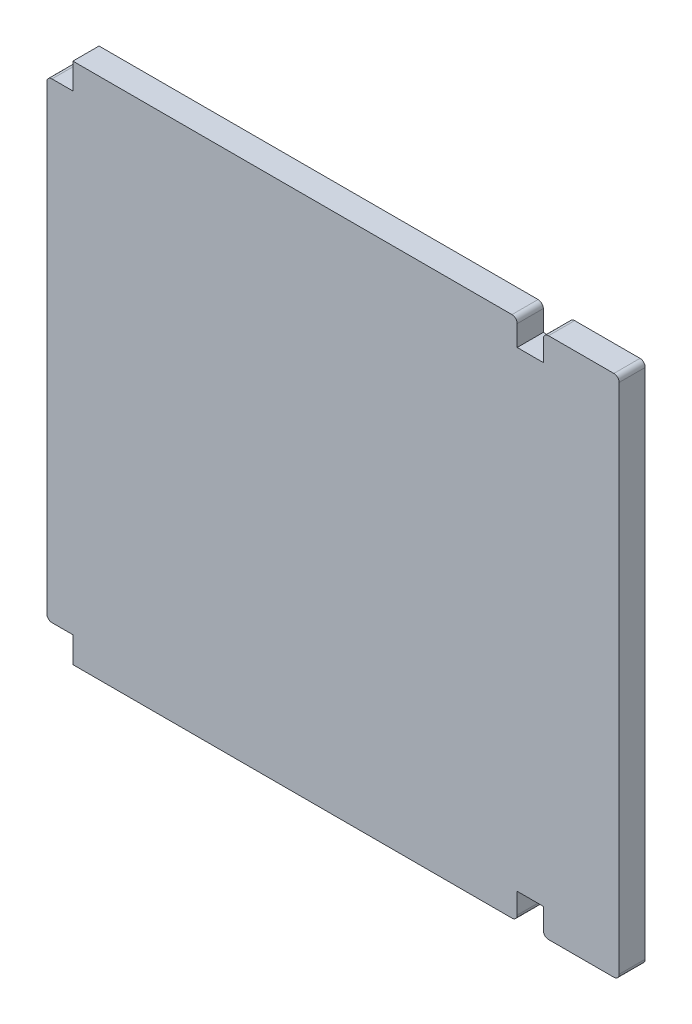
SolidWorks part; units mm, degrees
ref_plane "Front" through (0, 0, 0) normal (0, 0, 1) x (1, 0, 0)
ref_plane "Top" through (0, 0, 0) normal (0, 1, 0) x (1, 0, 0)
ref_plane "Right" through (0, 0, 0) normal (1, 0, 0) x (0, 0, -1)
sketch "Sketch1" plane through (0, 0, 0) normal (0, 0, 1) x (1, 0, 0)
  line L0 (0, 95.05) -> (0, 100)
  line L1 (0, 0) -> (85, 0)
  line L2 (0, 0) -> (0, 4.95)
  line L3 (0, 100) -> (85, 100)
  line L4 (85, 0) -> (85, 4.95)
  line L5 (0, 95.05) -> (-5, 95.05)
  line L7 (0, 4.95) -> (-5, 4.95)
  line L8 (-5, 95.05) -> (-5, 4.95)
  line L9 (85, 95.05) -> (90, 95.05)
  line L11 (85, 4.95) -> (90, 4.95)
  line L13 (85, 95.05) -> (85, 100)
  line L14 (90, 100) -> (90, 95.05)
  line L15 (90, 100) -> (104.5, 100)
  line L16 (90, -0.05) -> (104.5, -0.05)
  line L17 (104.5, 100) -> (104.5, -0.05)
  line L18 (90, 4.95) -> (90, -0.05)
  dimension "D1" = 85
  dimension "D2" = 4.95
  dimension "D3" = 4.95
  dimension "D4" = 4.95
  dimension "D5" = 5
  dimension "D6" = 100
  dimension "D7" = 4.95
  dimension "D10" = 14.5
extrude "Boss-Extrude1" add sketch "Sketch1" along normal blind 5
fillet "Fillet1" radius 1 8 edges at (104.5, -0.05, 2.5) (104.5, 100, 2.5) (85, 100, 2.5) (90, 100, 2.5) (-5, 95.05, 2.5) (-5, 4.95, 2.5) (85, 0, 2.5) (90, -0.05, 2.5)
